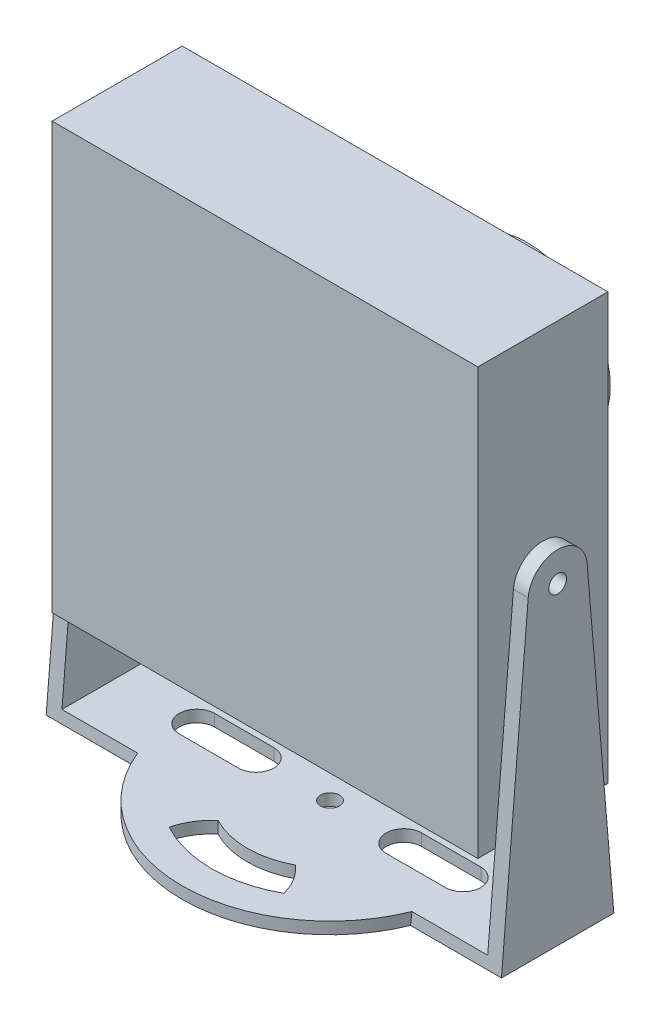
SolidWorks part; units mm, degrees
ref_plane "前视基准面" through (0, 0, 0) normal (0, 0, 1) x (1, 0, 0)
ref_plane "上视基准面" through (0, 0, 0) normal (0, 1, 0) x (1, 0, 0)
ref_plane "右视基准面" through (0, 0, 0) normal (1, 0, 0) x (0, 0, -1)
sketch "草图1" plane through (0, 0, 0) normal (0, 0, 1) x (1, 0, 0)
  line L1 (-18, 18) -> (18, 18)
  line L2 (-18, 18) -> (-18, -18)
  line L3 (-18, -18) -> (18, -18)
  line L4 (18, 18) -> (18, -18)
  line L5 (-18, 18) -> (18, -18) construction
  line L6 (-18, -18) -> (18, 18) construction
  point P0 (0, 0)
  dimension "D1" = 36
  dimension "D2" = 36
extrude "凸台-拉伸1" add sketch "草图1" along normal blind 11
sketch "草图2" plane through (0, 0, 0) normal (0, 0, -1) x (-1, 0, 0)
  line L0 (0, 0) -> (0, -19.8687) construction
  line L1 (-16, 16) -> (16, 16)
  line L2 (-16, 16) -> (-16, -16)
  line L3 (-16, -16) -> (16, -16)
  line L4 (16, 16) -> (16, -16)
  line L5 (-16, 16) -> (16, -16) construction
  line L6 (-16, -16) -> (16, 16) construction
  circle A0 centre (-14, 14) radius 1.25
  circle A1 centre (14, -14) radius 1.25
  circle A2 centre (14, 14) radius 1.25
  circle A3 centre (-14, -14) radius 1.25
  point P0 (0, 0)
  dimension "D2" = 2.5
  dimension "D1" = 32
  dimension "D3" = 2
extrude "凸台-拉伸2" add sketch "草图2" along normal blind 2
sketch "草图3" plane through (0, 0, 0) normal (0, 0, -1) x (-1, 0, 0)
  circle A0 centre (0, 0) radius 7
  dimension "D1" = 14
extrude "凸台-拉伸3" add sketch "草图3" along normal blind 22.2 from surface at -11 starting at face at (0, 0, 11)
sketch "草图4" plane through (0, 0, 0) normal (1, 0, 0) x (0, 0, -1)
  line L0 (0, 0) -> (22.179, 0) construction
  line L1 (0, -18) -> (0, 18) construction
  line L2 (11.2, 7) -> (2, 7) construction
  line L3 (8.5, 8) -> (9.5, 8)
  line L4 (8.5, 8) -> (8.5, 6)
  line L5 (8.5, 6) -> (9.5, 6)
  line L6 (9.5, 8) -> (9.5, 6)
  line L7 (8.5, 8) -> (9.5, 6) construction
  line L8 (8.5, 6) -> (9.5, 8) construction
  line L9 (11.2, -7) -> (11.2, 7) construction
  point P4 (9, 7)
  dimension "D1" = 2
  dimension "D2" = 1
  dimension "D3" = 2.2
revolve "切除-旋转1" cut sketch "草图4" angle 360 about L0
sketch "草图5" plane through (0, 0, -11.2) normal (0, 0, -1) x (-1, 0, 0)
  circle A0 centre (0, 0) radius 5
  dimension "D1" = 10
extrude "切除-拉伸1" cut sketch "草图5" against normal blind 0.9
sketch "草图6" plane through (0, 0, 0) normal (1, 0, 0) x (0, 0, -1)
  line L0 (-7.9911, 0.2107) -> (-10.25, -26.5)
  line L1 (-10.25, -26.5) -> (-0.75, -26.5)
  line L2 (-0.75, -26.5) -> (-3.0089, 0.2107)
  line L3 (-11, 18) -> (0, 18) construction
  line L4 (-5.5, 0) -> (-5.5, 5.415) construction
  circle A0 centre (-5.5, 0) radius 0.75
  circle A1 centre (-5.5, 0) radius 2.5
  point P10 (-5.5, 18)
  point P11 (-8, 0)
  point P13 (-3.0252, 0.3541)
  point P14 (-8, 0)
  point P15 (-8.1475, -1.6387)
  dimension "D1" = 1.5
  dimension "D3" = 5
  dimension "D4" = 29
  dimension "D2" = 9.5
extrude "凸台-拉伸4" add sketch "草图6" against normal up to surface (1.25 mm away) from offset 19.25
sketch "草图7" plane through (18, 0, 0) normal (-1, 0, 0) x (0, 0, 1)
  line L0 (0.8346, -25.5) -> (10.1654, -25.5)
  line L1 (0.75, -26.5) -> (1.4688, -18) construction
  line L2 (9.5312, -18) -> (10.25, -26.5) construction
  line L3 (10.25, -26.5) -> (0.75, -26.5) construction
  line L4 (10.25, -26.5) -> (0.75, -26.5)
  line L5 (0.75, -26.5) -> (0.8346, -25.5)
  line L6 (10.1654, -25.5) -> (10.25, -26.5)
  dimension "D1" = 1
extrude "凸台-拉伸5" add sketch "草图7" along normal blind 37.25
sketch "草图9" plane through (0, -26.5, 0) normal (0, -1, 0) x (1, 0, 0)
  line L1 (0, 0) -> (0, 15.5) construction
  line L2 (0, 5.5) -> (-21.2545, 5.5) construction
  circle A0 centre (0, 5.5) radius 12.5
  arc A1 (4.8509, 14.2446) -> (-4.8509, 14.2446) centre (0, 5.5) ccw
  arc A2 (3.274, 11.6871) -> (-3.274, 11.6871) centre (0, 5.5) ccw
  arc A3 (-4.8509, 14.2446) -> (-3.274, 11.6871) centre (0, 15.4707) ccw
  arc A4 (4.8509, 14.2446) -> (3.274, 11.6871) centre (0, 15.4707) cw
  arc A5 (-4.8509, -3.2446) -> (-3.274, -0.6871) centre (0, -4.4707) cw
  arc A6 (4.8509, -3.2446) -> (3.274, -0.6871) centre (0, -4.4707) ccw
  arc A7 (3.274, -0.6871) -> (-3.274, -0.6871) centre (0, 5.5) cw
  arc A8 (4.8509, -3.2446) -> (-4.8509, -3.2446) centre (0, 5.5) cw
  circle A9 centre (0, 5.5) radius 1
  dimension "D1" = 25
  dimension "D2" = 20
  dimension "D3" = 14
  dimension "D4" = 5.0035
  dimension "D5" = 2
extrude "凸台-拉伸6" add sketch "草图9" against normal up to surface (1 mm away) up to face at (-0.625, -25.5, 5.5)
sketch "草图8" plane through (0, -26.5, 0) normal (0, -1, 0) x (1, 0, 0)
  line L0 (6.25, 5.5) -> (11.25, 5.5) construction
  line L1 (6.25, 7) -> (11.25, 7)
  line L2 (6.25, 4) -> (11.25, 4)
  line L4 (19.25, 10.25) -> (19.25, 0.75) construction
  arc A0 (6.25, 7) -> (6.25, 4) centre (6.25, 5.5) ccw
  arc A1 (11.25, 4) -> (11.25, 7) centre (11.25, 5.5) ccw
  point P2 (8.75, 5.5)
  point P10 (6.3192, 5.5)
  dimension "D1" = 8
  dimension "D2" = 1.5
  dimension "D3" = 8
extrude "切除-拉伸2" cut sketch "草图8" against normal blind 2
sketch "草图10" plane through (-18, 0, 0) normal (-1, 0, 0) x (0, 0, 1)
  line L3 (3.0089, 0.2107) -> (0.75, -26.5)
  line L4 (10.25, -26.5) -> (7.9911, 0.2107)
  line L5 (0.75, -26.5) -> (10.25, -26.5)
  line L6 (3.0089, 0.2107) -> (0.75, -26.5)
  line L7 (10.25, -26.5) -> (7.9911, 0.2107)
  line L8 (0.75, -26.5) -> (10.25, -26.5)
  circle A0 centre (5.5, 0) radius 0.75 construction
  arc A1 (7.9911, 0.2107) -> (3.0089, 0.2107) centre (5.5, 0) ccw
  arc A2 (7.9911, 0.2107) -> (3.0089, 0.2107) centre (5.5, 0) ccw
  circle A3 centre (5.5, 0) radius 0.75
  dimension "D1" = 0
extrude "凸台-拉伸7" add sketch "草图10" along normal blind 1.25
mirror "镜向3" about plane through (0, 0, 0) normal (1, 0, 0) of "切除-拉伸2"
hole_wizard "M2 螺纹孔的螺纹孔钻头1" positions "草图11" profile "草图12" hole size "M2" standard "GB"
sketch "草图11" plane through (0, -26.5, 0) normal (0, -1, 0) x (-1, 0, 0)
  point P0 (0, -5.5)
sketch "草图12" plane through (0, -26.5, 5.5) normal (1, 0, 0) x (0, 0, -1)
  line L0 (0, 0) -> (0, 2.4807)
  line L1 (0, 2.4807) -> (0.8, 2)
  line L2 (0.8, 2) -> (0.8, 0)
  line L5 (0.8, 0) -> (0, 0)
  line L10 (0, 2.4807) -> (-0.8, 2) construction
  line L11 (0, -6.35) -> (0, 107.95) construction
  dimension "孔直径" = 1.6
  dimension "孔深度" = 2
  dimension "导头角度" = 118
